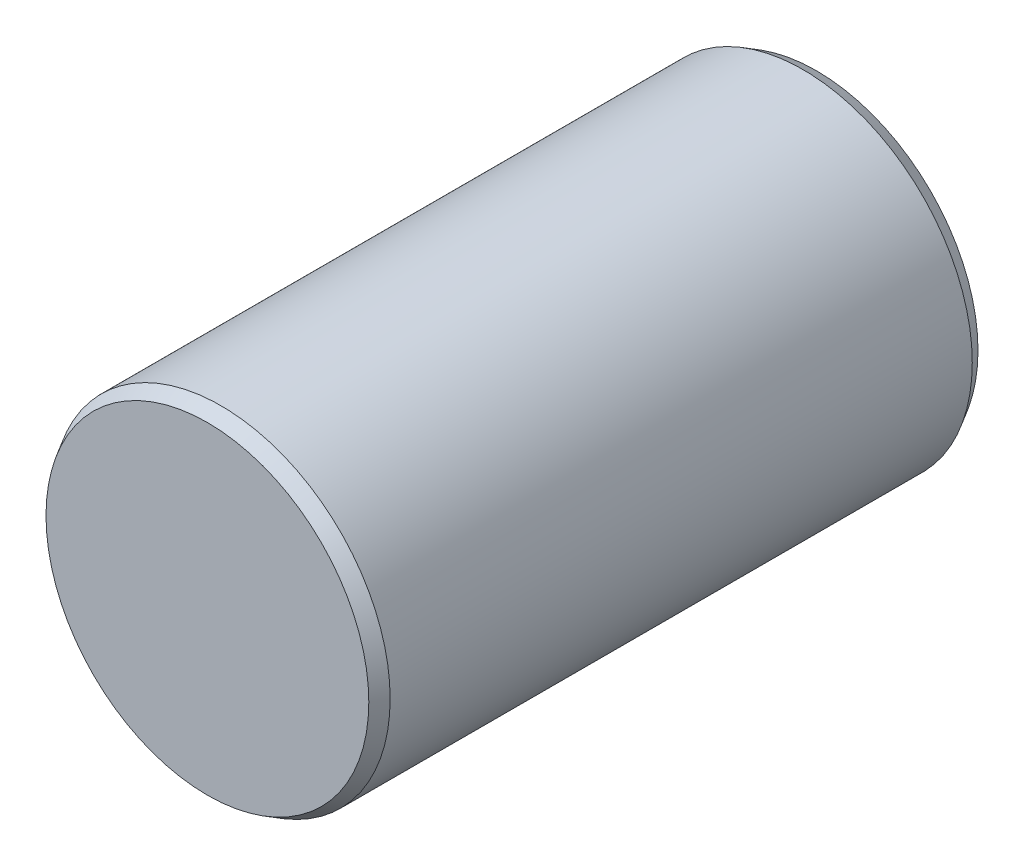
SolidWorks part; units mm, degrees
material "1023 Tôle d'acier au carbone (SS)"
ref_plane "Plan de face" through (0, 0, 0) normal (0, 0, 1) x (1, 0, 0)
ref_plane "Plan de dessus" through (0, 0, 0) normal (0, 1, 0) x (1, 0, 0)
ref_plane "Plan de droite" through (0, 0, 0) normal (1, 0, 0) x (0, 0, -1)
sketch "Esquisse1" plane through (0, 0, 0) normal (0, 0, 1) x (1, 0, 0)
  circle A0 centre (0, 0) radius 2.5
  dimension "D1" = 5
extrude "Boss.-Extru.1" add sketch "Esquisse1" along normal mid plane 9
chamfer "Chanfrein1" distance 0.2 angle 30 2 edges at (2.5, 0, -4.5) (2.5, 0, 4.5)
